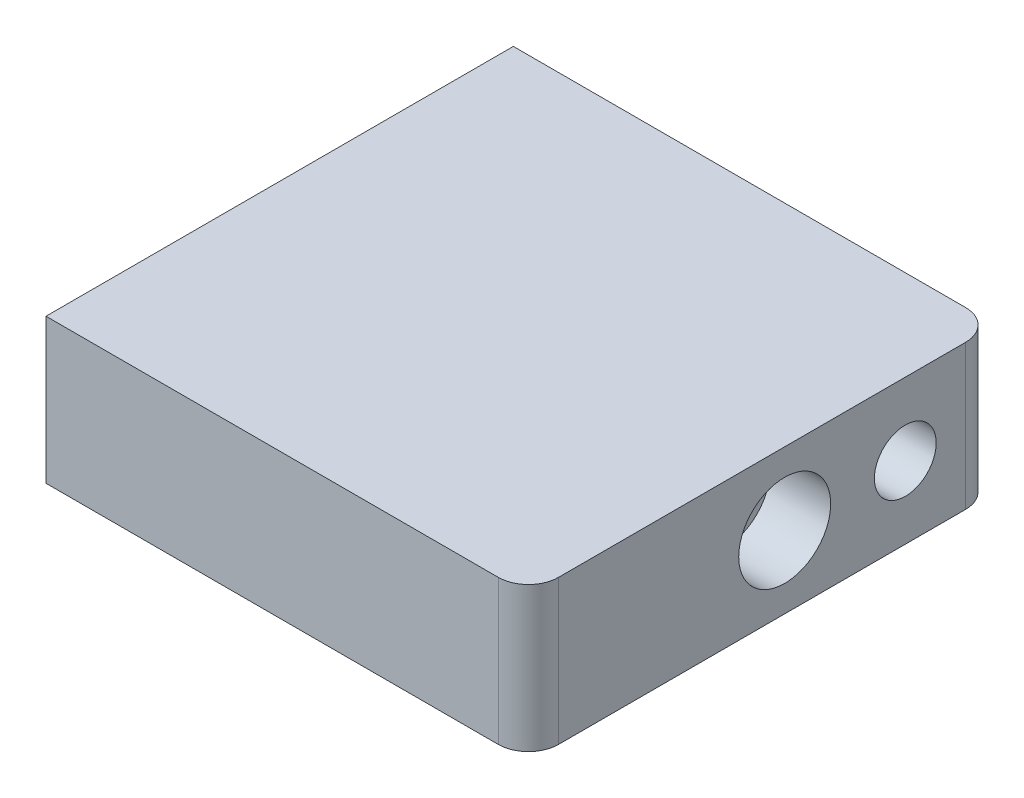
SolidWorks part; units mm, degrees
ref_plane "Front Plane" through (0, 0, 0) normal (0, 0, 1) x (1, 0, 0)
ref_plane "Top Plane" through (0, 0, 0) normal (0, 1, 0) x (1, 0, 0)
ref_plane "Right Plane" through (0, 0, 0) normal (1, 0, 0) x (0, 0, -1)
sketch "Sketch1" plane through (0, 0, 0) normal (0, 1, 0) x (1, 0, 0)
  line L0 (0, 0) -> (0, 77.5)
  line L5 (0, 77.5) -> (80, 77.5)
  line L6 (80, 77.5) -> (80, 0)
  line L7 (80, 0) -> (0, 0)
  dimension "D1" = 77.5
  dimension "D2" = 80
extrude "Boss-Extrude1" add sketch "Sketch1" along normal blind 24
sketch "Sketch2" plane through (80, 0, 0) normal (1, 0, 0) x (0, 0, -1)
  line L0 (77.5, 0) -> (77.5, 24) construction
  line L1 (77.5, 12) -> (0, 12) construction
  line L3 (77.5, 24) -> (77.5, 0) construction
  line L4 (0, 24) -> (0, 0) construction
  circle A0 centre (62.5, 12) radius 5.125
  circle A1 centre (42.5, 12) radius 7.625
  dimension "D1" = 10.25
  dimension "D3" = 15.25
  dimension "D2" = 15
  dimension "D4" = 20
extrude "Cut-Extrude1" cut sketch "Sketch2" against normal blind 10 from surface at 0 starting at face at (80, 12, -38.75)
fillet "Fillet1" radius 5 2 edges at (80, 12, 0) (80, 12, -77.5)
